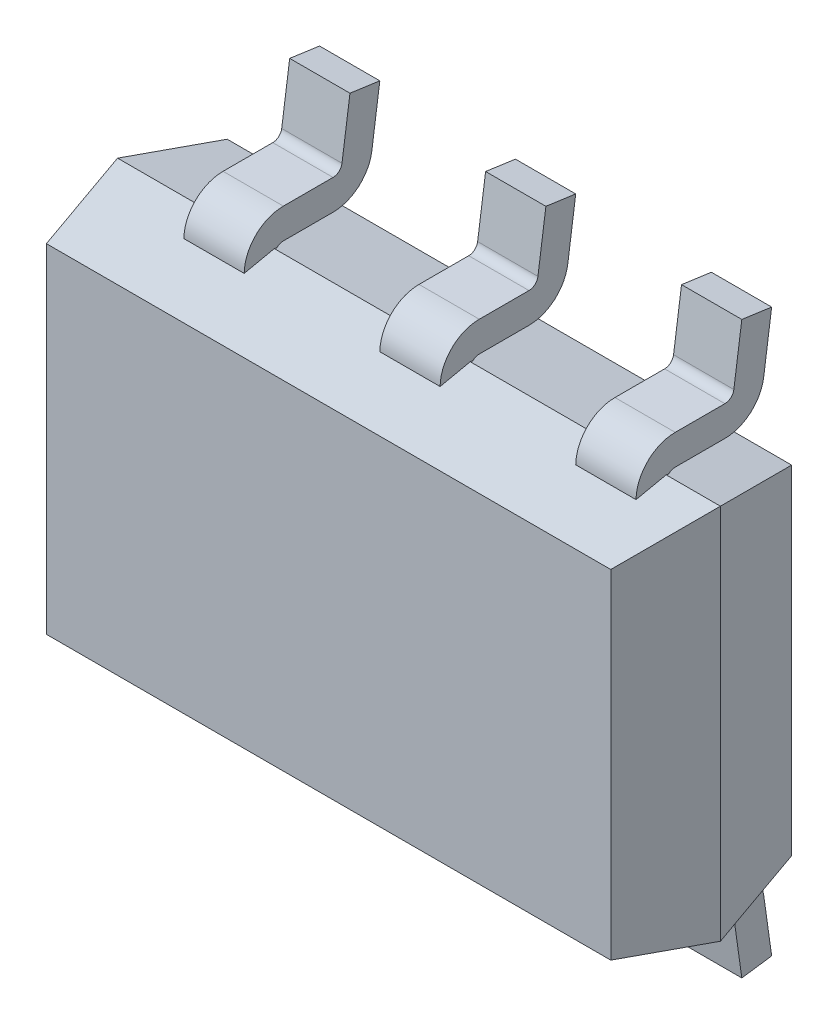
SolidWorks part; units mm, degrees
ref_plane "Front Plane" through (0, 0, 0) normal (0, 0, 1) x (1, 0, 0)
ref_plane "Top Plane" through (0, 0, 0) normal (0, 1, 0) x (1, 0, 0)
ref_plane "Right Plane" through (0, 0, 0) normal (1, 0, 0) x (0, 0, -1)
sketch "Sketch1" plane through (0, 0, 0) normal (0, 0, 1) x (1, 0, 0)
  line L1 (0, 0) -> (2, 0)
  line L2 (0, 0) -> (0, 1.25)
  line L3 (0, 1.25) -> (2, 1.25)
  line L4 (2, 0) -> (2, 1.25)
  dimension "D1" = 1.25
  dimension "D2" = 2
extrude "Boss-Extrude1" add sketch "Sketch1" along normal blind 0.3 draft 12
sketch "Sketch2" plane through (0, 0, 0) normal (0, 0, -1) x (-1, 0, 0)
  line L1 (-2, 1.25) -> (0, 1.25)
  line L2 (-2, 1.25) -> (-2, 0)
  line L3 (-2, 0) -> (0, 0)
  line L4 (0, 1.25) -> (0, 0)
extrude "Boss-Extrude2" add sketch "Sketch2" along normal blind 0.3 draft 12
ref_plane "Plane1" through (0.42, 0, 0) normal (1, 0, 0) x (0, 0, -1)
sketch "Sketch4" plane through (0.42, 0, 0) normal (1, 0, 0) x (0, 0, -1)
  line L0 (0, 1.2181) -> (0, 1.2572)
  line L1 (0, 0) -> (0, 1.25) construction
  line L2 (0, 1.2572) -> (0.3078, 1.2572)
  line L3 (0.3078, 1.2572) -> (0.35, 1.5572)
  line L4 (0.3, 1.1862) -> (0.3, 0.0638) construction
  dimension "D1" = 0.3
  dimension "D2" = 8
  dimension "D3" = 0.05
extrude "Extrude-Thin1" add sketch "Sketch4" along normal mid plane 0.2 thin thin type one direction reverse wall 0.1
pattern_linear "LPattern1" count 3 spacing 0.65 along (1, 0, 0) skipping (1, 0) of "Extrude-Thin1"
ref_plane "Plane2" through (0, 0.625, 0) normal (0, 1, 0) x (1, 0, 0)
mirror "Mirror1" about plane through (0, 0.625, 0) normal (0, 1, 0) of "LPattern1", "Extrude-Thin1"
pattern_linear "LPattern2" count 2 spacing 0.65 along (1, 0, 0) of "Extrude-Thin1"
